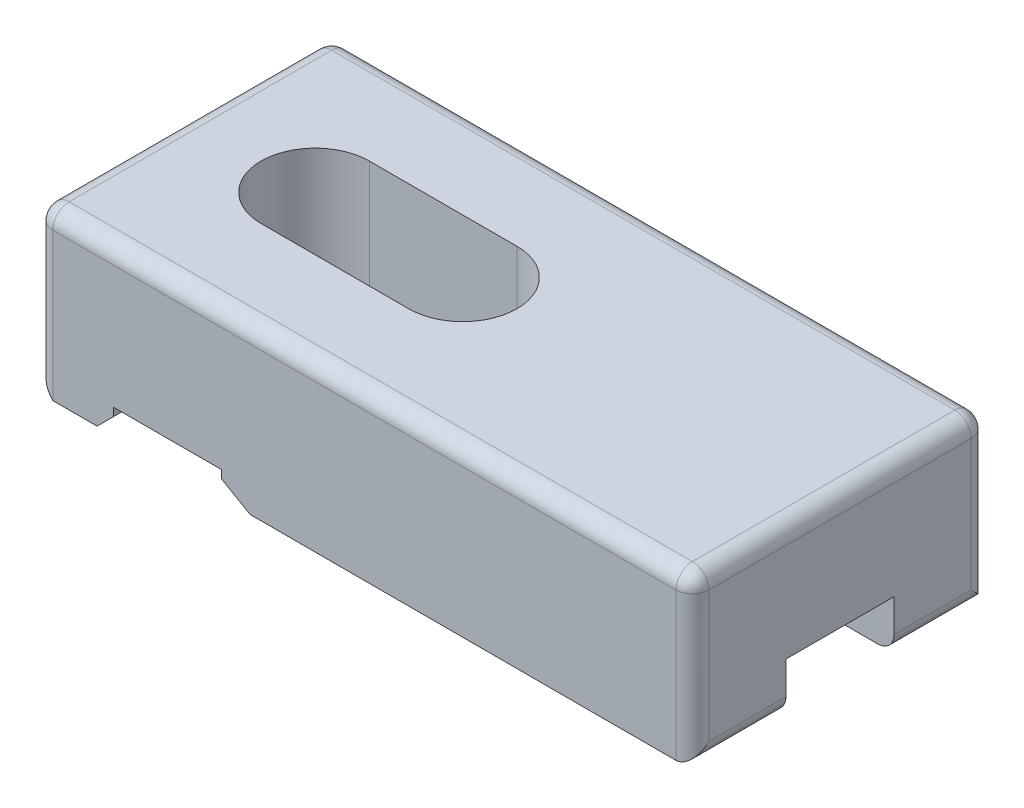
SolidWorks part; units mm, degrees
material "AISI 1045 钢，冷拔"
ref_plane "前视基准面" through (0, 0, 0) normal (0, 0, 1) x (1, 0, 0)
ref_plane "上视基准面" through (0, 0, 0) normal (0, 1, 0) x (1, 0, 0)
ref_plane "右视基准面" through (0, 0, 0) normal (1, 0, 0) x (0, 0, -1)
sketch "草图1" plane through (0, 0, 0) normal (0, 1, 0) x (1, 0, 0)
  line L0 (17, 9) -> (8, 9) construction
  line L1 (0, 0) -> (40, 0)
  line L2 (0, 0) -> (0, 18)
  line L3 (0, 18) -> (40, 18)
  line L4 (40, 0) -> (40, 18)
  line L5 (17, 5.7) -> (8, 5.7)
  line L6 (17, 12.3) -> (8, 12.3)
  arc A0 (17, 5.7) -> (17, 12.3) centre (17, 9) ccw
  arc A1 (8, 12.3) -> (8, 5.7) centre (8, 9) ccw
  point P7 (12.5, 9)
  dimension "D5" = 3.3
  dimension "D1" = 40
  dimension "D2" = 18
  dimension "D3" = 17
  dimension "D4" = 9
  dimension "D6" = 9
extrude "凸台-拉伸1" add sketch "草图1" along normal blind 10
sketch "草图2" plane through (0, 0, 0) normal (0, -1, 0) x (1, 0, 0)
  line L2 (40, 0) -> (40, -18) construction
  line L3 (40, -5.7) -> (40, -12.3)
  line L4 (40, -12.3) -> (8, -12.3)
  line L13 (8, -5.7) -> (40, -5.7)
  arc A0 (8, -5.7) -> (8, -12.3) centre (8, -9) ccw
  point P0 (0, 0)
  dimension "D1" = 3.3
extrude "切除-拉伸1" cut sketch "草图2" against normal blind 3
sketch "草图3" plane through (0, 0, 0) normal (0, -1, 0) x (1, 0, 0)
  line L0 (0, -5.7) -> (4.7, -5.7)
  line L1 (0, -18) -> (0, 0) construction
  line L3 (0, -12.3) -> (4.7, -12.3)
  line L4 (4.7, 0) -> (4.7, -5.7)
  line L5 (0, 0) -> (40, 0) construction
  line L6 (40, -18) -> (0, -18) construction
  line L7 (11.3, 0) -> (11.3, -18)
  line L8 (4.7, -12.3) -> (4.7, -18)
  line L9 (4.7, 0) -> (11.3, 0)
  line L10 (4.7, -18) -> (11.3, -18)
  line L11 (0, -5.7) -> (0, -12.3)
  dimension "D1" = 6.6
  dimension "D2" = 6.6
  dimension "D3" = 5.7
  dimension "D4" = 4.7
extrude "切除-拉伸2" cut sketch "草图3" against normal blind 1.5
chamfer "倒角1" distance 1 angle 45 4 edges at (0, 0, -15.15) (4.7, 0, -15.15) (4.7, 0, -2.85) (0, 0, -2.85)
chamfer "倒角2" distance 1 angle 60 2 edges at (11.3, 0, -15.15) (11.3, 0, -2.85)
fillet "圆角1" radius 1 10 edges at (20, 10, -18) (40, 10, -9) (20, 10, 0) (0, 10, -9) (40, 5, 0) (40, 5, -18) (0, 5.5, -18) (0, 5.5, 0) (40, 0, -15.15) (40, 0, -2.85)
